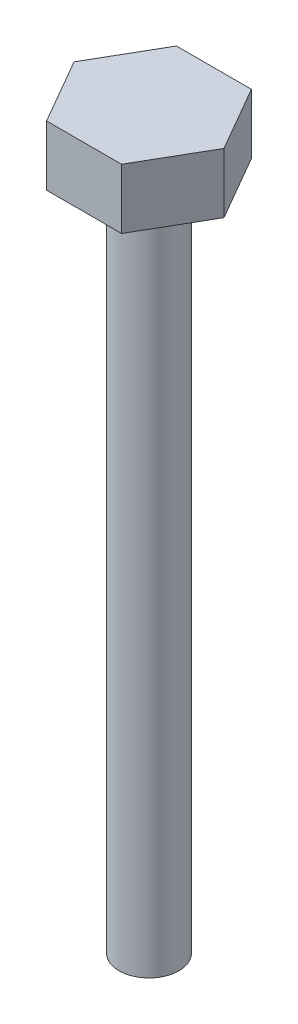
SolidWorks part; units mm, degrees
ref_plane "Alzado" through (0, 0, 0) normal (0, 0, 1) x (1, 0, 0)
ref_plane "Planta" through (0, 0, 0) normal (0, 1, 0) x (1, 0, 0)
ref_plane "Vista lateral" through (0, 0, 0) normal (1, 0, 0) x (0, 0, -1)
sketch "Croquis1" plane through (0, 0, 0) normal (0, 1, 0) x (1, 0, 0)
  line L1 (5, 0) -> (2.5, 4.3301)
  line L2 (2.5, 4.3301) -> (-2.5, 4.3301)
  line L3 (-2.5, 4.3301) -> (-5, 0)
  line L4 (-5, 0) -> (-2.5, -4.3301)
  line L5 (-2.5, -4.3301) -> (2.5, -4.3301)
  line L6 (2.5, -4.3301) -> (5, 0)
  circle A0 centre (0, 0) radius 4.3301 construction
  dimension "D1" = 5
extrude "Saliente-Extruir1" add sketch "Croquis1" along normal blind 4
sketch "Croquis2" plane through (0, 0, 0) normal (0, -1, 0) x (1, 0, 0)
  circle A0 centre (0, 0) radius 2
  dimension "D1" = 4
extrude "Saliente-Extruir2" add sketch "Croquis2" along normal blind 45
